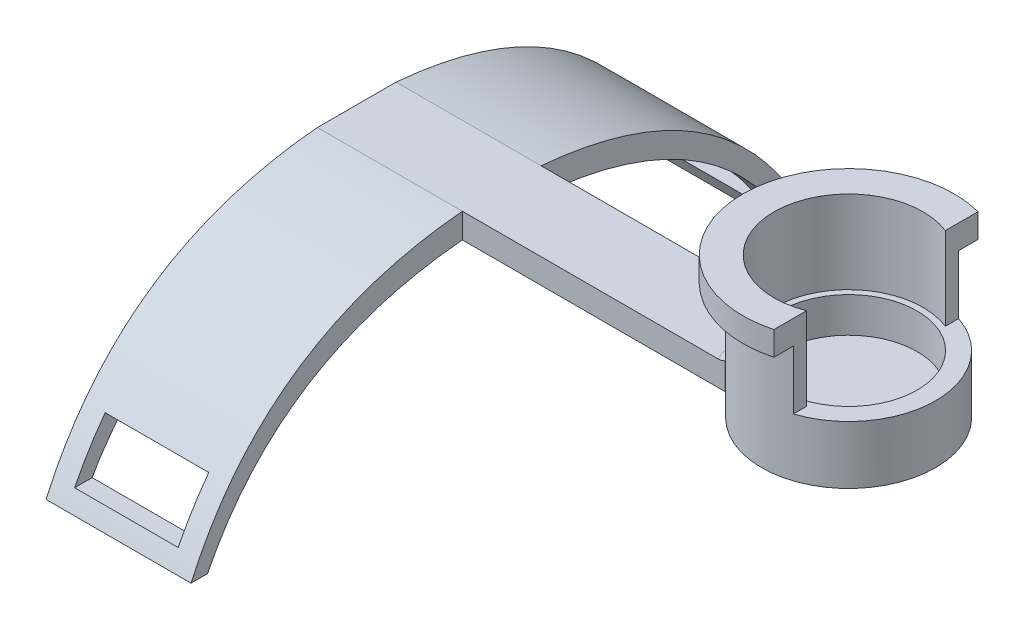
SolidWorks part; units mm, degrees
ref_plane "Front Plane" through (0, 0, 0) normal (0, 0, 1) x (1, 0, 0)
ref_plane "Top Plane" through (0, 0, 0) normal (0, 1, 0) x (1, 0, 0)
ref_plane "Right Plane" through (0, 0, 0) normal (1, 0, 0) x (0, 0, -1)
sketch "0.1mm fit for pot" plane through (0, 0, 0) normal (0, 1, 0) x (1, 0, 0)
  circle A1 centre (0, 0) radius 10.5
  dimension "D2" = 21
extrude "Boss-Extrude1" add sketch "0.1mm fit for pot" along normal blind 2.75
sketch "Sketch4" plane through (0, 2.75, 0) normal (0, 1, 0) x (1, 0, 0)
  circle A0 centre (0, 0) radius 8.275
  circle A1 centre (0, 0) radius 10.5 construction
  circle A2 centre (0, 0) radius 10.5
  dimension "D1" = 16.55
extrude "Boss-Extrude2" add sketch "Sketch4" along normal blind 4.25
sketch "Sketch5" plane through (0, 2.75, 0) normal (0, 1, 0) x (1, 0, 0)
  line L6 (-1, -8.2144) -> (-1, -7.0658)
  line L7 (-1, -7.0658) -> (0.9881, -7.0658)
  line L8 (0.9881, -7.0658) -> (0.9881, -8.2158)
  circle A0 centre (0, 0) radius 8.275 construction
  arc A1 (-1, -8.2144) -> (0.9881, -8.2158) centre (0, 0) ccw
  point P3 (0, -8.25)
  point P6 (0, -8.25)
  point P7 (0, -8.25)
  dimension "D1" = 1.15
extrude "Boss-Extrude3" add sketch "Sketch5" along normal blind 2
fillet "Fillet1" radius 0.25 5 edges at (-1, 4.75, 7.6401) (0.9881, 4.75, 7.6408) (0.9881, 3.75, 7.0658) (-0.006, 4.75, 7.0658) (-1, 3.75, 7.0658)
sketch "Sketch7" plane through (0, 7, 0) normal (0, 1, 0) x (1, 0, 0)
  line L0 (3.2996, 9.9681) -> (3.2996, 8.3733)
  line L1 (3.2996, -8.3733) -> (3.2996, -9.9681)
  arc A0 (3.2996, 9.9681) -> (3.2996, -9.9681) centre (0, 0) ccw
  arc A1 (3.2996, 8.3733) -> (3.2996, -8.3733) centre (0, 0) ccw
  dimension "D1" = 18
  dimension "D2" = 21
extrude "Boss-Extrude6" add sketch "Sketch7" along normal blind 10
sketch "Sketch8" plane through (0, 17, 0) normal (0, 1, 0) x (1, 0, 0)
  line L0 (3.2996, 12.3156) -> (3.2996, 9.9681)
  line L1 (3.2996, -9.9681) -> (3.2996, -12.3156)
  arc A0 (3.2996, 12.3156) -> (3.2996, -12.3156) centre (0, 0) ccw
  arc A1 (3.2996, 9.9681) -> (3.2996, -9.9681) centre (0, 0) ccw construction
  arc A2 (3.2996, 9.9681) -> (3.2996, -9.9681) centre (0, 0) ccw
  dimension "D1" = 2.25
extrude "Boss-Extrude7" add sketch "Sketch8" against normal blind 2.9
sketch "Sketch9" plane through (0, 0, 0) normal (0, -1, 0) x (1, 0, 0)
  line L3 (-9.3642, 4.75) -> (-59.3642, 4.75)
  line L5 (-9.3642, -4.75) -> (-59.3642, -4.75)
  line L6 (-59.3642, 4.75) -> (-59.3642, -4.75)
  circle A0 centre (0, 0) radius 10.5 construction
  arc A1 (-9.3642, 4.75) -> (-9.3642, -4.75) centre (0, 0) ccw
  point P10 (-5.25, 0)
  dimension "D1" = 50
extrude "Boss-Extrude8" add sketch "Sketch9" against normal blind 3
fillet "Fillet2" radius 1.5 3 edges at (-9.3642, 1.5, -4.75) (-9.3642, 1.5, 4.75) (-10.5, 3, 0)
sketch "Sketch10" plane through (-59.3642, 0, 0) normal (-1, 0, 0) x (0, 0, 1)
  line L0 (0, 3) -> (0, -19.5) construction
  line L1 (4.75, 3) -> (-4.75, 3) construction
  line L2 (37.5, -19.5) -> (-37.5, -19.5) construction
  line L3 (-37.5, -19.5) -> (-35.5, -19.5)
  line L4 (37.5, -19.5) -> (35.5, -19.5)
  line L5 (-4.75, 3) -> (4.75, 3)
  line L6 (4.75, 0) -> (-4.75, 0)
  spline S0 degree 2 poles (-37.5, -19.5) (-28.3868, 0.9123) (-4.75, 3) knots 0 0 0 0.454443 0.454443 0.454443
  spline S1 degree 2 poles (35.5, -19.5) (26.7622, -1.9487) (4.75, 0) knots 0 0 0 0.451407 0.451407 0.451407
  spline S2 degree 2 poles (4.75, 3) (28.3868, 0.9123) (37.5, -19.5) knots 0.545557 0.545557 0.545557 1 1 1
  spline S3 degree 2 poles (-4.75, 0) (-26.7622, -1.9487) (-35.5, -19.5) knots 0.548593 0.548593 0.548593 1 1 1
  point P8 (0, -19.5)
  dimension "D1" = 22.5
  dimension "D2" = 75
  dimension "D3" = 2
  dimension "D4" = 2
extrude "Boss-Extrude9" add sketch "Sketch10" against normal blind 17.5
sketch "Sketch11" plane through (0, 0, -4.75) normal (0, 0, -1) x (-1, 0, 0)
  line L0 (50.6142, -19.5) -> (50.6142, -17.5) construction
  line L1 (41.8642, -19.5) -> (59.3642, -19.5) construction
  line L2 (56.8642, -17.5) -> (44.3642, -17.5) construction
  line L4 (44.3642, -17.5) -> (56.8642, -17.5)
  line L5 (44.3642, -17.5) -> (44.3642, -11.5)
  line L6 (44.3642, -11.5) -> (56.8642, -11.5)
  line L7 (56.8642, -17.5) -> (56.8642, -11.5)
  point P7 (50.6142, -17.5)
  dimension "D1" = 12.5
  dimension "D2" = 6
  dimension "D3" = 2
extrude "Cut-Extrude1" cut sketch "Sketch11" against normal through all both and the other way through all
